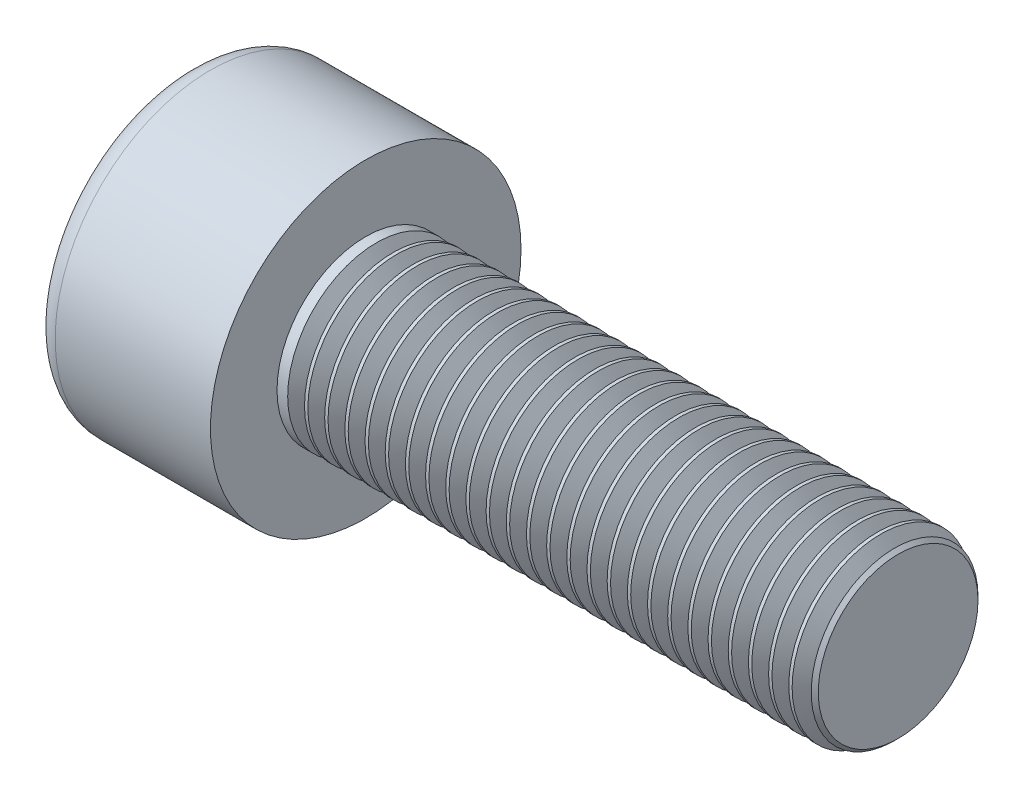
SolidWorks part; units mm, degrees
ref_plane "Front" through (0, 0, 0) normal (0, 0, 1) x (1, 0, 0)
ref_plane "Top" through (0, 0, 0) normal (0, 1, 0) x (1, 0, 0)
ref_plane "Right" through (0, 0, 0) normal (1, 0, 0) x (0, 0, -1)
sketch "Sketch1" plane through (0, 0, 0) normal (1, 0, 0) x (0, 0, -1)
  circle A0 centre (0, 0) radius 3.5
  dimension "dk" = 7
extrude "BaseHead" add sketch "Sketch1" along normal blind 4
sketch "Sketch2" plane through (4, 0, 0) normal (1, 0, 0) x (0, 0, -1)
  circle A0 centre (0, 0) radius 2
  dimension "d" = 4
extrude "BaseBody" add sketch "Sketch2" along normal blind 12
cosmetic thread "ThreadCosmetic1" [suppressed] parameters "b"=12, "D2"=3.242
sketch "Sketch3" plane through (0, 0, 0) normal (1, 0, 0) x (0, 0, -1)
  line L1 (1.7321, 0) -> (0.866, 1.5)
  line L2 (0.866, 1.5) -> (-0.866, 1.5)
  line L3 (-0.866, 1.5) -> (-1.7321, 0)
  line L4 (-1.7321, 0) -> (-0.866, -1.5)
  line L5 (-0.866, -1.5) -> (0.866, -1.5)
  line L6 (0.866, -1.5) -> (1.7321, 0)
  circle A0 centre (0, 0) radius 1.5 construction
  dimension "s" = 3
  dimension "e" = 3.4641
extrude "HexagonSocket" cut sketch "Sketch3" along normal blind 2
sketch "Sketch4" plane through (-4.1961, 0.75, 0) normal (0, 0, 1) x (-1, 0, 0)
  line L0 (-6.1961, 2.25) -> (-7.0622, 0.75)
  line L2 (-7.0622, 0.75) -> (-6.1961, 0.75)
  line L3 (-6.1961, 0.75) -> (-6.1961, 2.25)
  line L4 (-5.0351, 0.75) -> (0.839, 0.75) construction
  line L5 (-20.1961, 0.75) -> (-8.1961, 0.75) construction
  line L6 (-8.1961, 0.75) -> (-4.1961, 0.75) construction
  dimension "m" = 60
revolve "Cut-Revolve1" cut sketch "Sketch4" angle 360 about L4
fillet "HeadFillet" [suppressed] radius 0.2
fillet "TopFillet" radius 0.5 1 edges at (0, 0, -3.5)
chamfer "Chamfer1" distance 0.2 angle 45 1 edges at (16, 0, -2)
sketch "Sketch5" plane through (0, 0, 0) normal (0, 0, 1) x (1, 0, 0)
  line L0 (15.8, 1.6718) -> (15.9895, 2)
  line L1 (15.9895, 2) -> (15.9895, 2.379)
  line L2 (15.9895, 2.379) -> (15.6105, 2.379)
  line L3 (15.6105, 2.379) -> (15.6105, 2)
  line L4 (15.6105, 2) -> (15.8, 1.6718)
  line L5 (0, 0) -> (7.8886, 0) construction
  line L6 (15.8, -2) -> (15.8, 2) construction
  dimension "D1" = 4
  dimension "D2" = 0.379
revolve "Cut-Revolve10" cut sketch "Sketch5" angle 360 about L5
pattern_linear "LPattern10" count 26 spacing 0.4548 along (-1, 0, 0) of "Cut-Revolve10"
equation "\"r1@TopFillet\" = \"d@Sketch2\" / 8"
equation "\"D1@Chamfer1\" = \"r@HeadFillet\""
equation "\"D1@Sketch5\" = \"d@Sketch2\""
equation "\"D2@Sketch5\" =  ( \"d@Sketch2\" - \"D2@ThreadCosmetic1\" )  / 2"
equation "\"D3@LPattern10\" = \"D2@Sketch5\" * 1.2"
equation "\"D1@LPattern10\" = \"b@ThreadCosmetic1\" / \"D3@LPattern10\""
